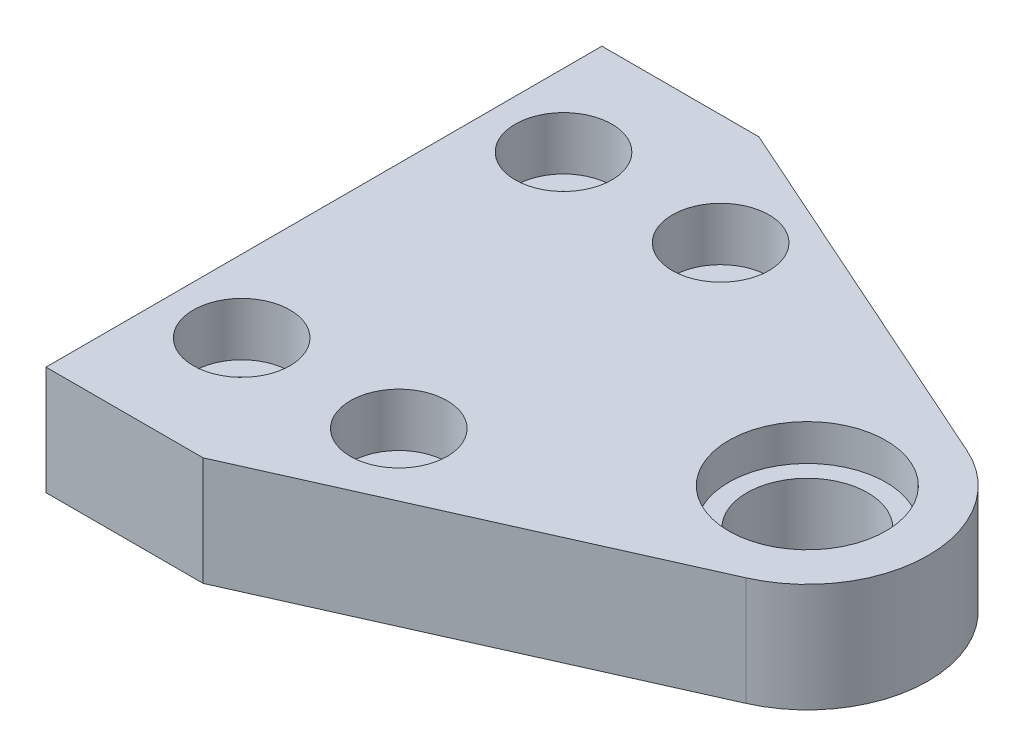
SolidWorks part; units mm, degrees
ref_plane "정면" through (0, 0, 0) normal (0, 0, 1) x (1, 0, 0)
ref_plane "윗면" through (0, 0, 0) normal (0, 1, 0) x (1, 0, 0)
ref_plane "우측면" through (0, 0, 0) normal (1, 0, 0) x (0, 0, -1)
sketch "스케치1" plane through (0, 0, 0) normal (0, 1, 0) x (1, 0, 0)
  line L0 (0, 0) -> (0, 23)
  line L1 (0, 23) -> (13, 23)
  line L2 (13, 23) -> (44.0753, 9.1319)
  line L4 (44.0753, -9.1319) -> (13, -23)
  line L5 (13, -23) -> (0, -23)
  line L6 (0, -23) -> (0, 0)
  arc A0 (44.0753, -9.1319) -> (44.0753, 9.1319) centre (40, 0) ccw
  point P10 (0, 0)
  point P11 (0, 0)
  point P12 (0, 0)
  point P13 (0, 0)
  point P14 (0, 0)
  point P15 (0, 0)
  point P16 (0, 0)
  point P17 (0, 0)
  point P18 (42.51, 0)
  point P19 (0, 0)
  point P20 (0, 0)
  point P21 (0, 0)
  dimension "D3" = 20
  dimension "D1" = 13
  dimension "D2" = 13
  dimension "D4" = 23
  dimension "D5" = 40
extrude "보스-돌출1" add sketch "스케치1" along normal blind 9
sketch "스케치2" plane through (0, 0, 0) normal (0, -1, 0) x (1, 0, 0)
  line L0 (0, -23) -> (0, 23) construction
  line L1 (0, -5) -> (24, -5)
  line L2 (0, -5) -> (0, 5)
  line L3 (0, 5) -> (24, 5)
  line L4 (24, -5) -> (24, 5)
  dimension "D1" = 5
  dimension "D2" = 10
  dimension "D3" = 24
extrude "보스-돌출2" add sketch "스케치2" along normal blind 3
hole_wizard "M4 소켓 머리 캡 나사용 카운터보어1" positions "스케치3" profile "스케치4" counterbore size "M4" standard "KS"
sketch "스케치3" plane through (0, 9, 0) normal (0, 1, 0) x (1, 0, 0)
  line L0 (0, 23) -> (0, -23) construction
  point P0 (6, 13.8271)
  point P2 (19, 13.8271)
  point P4 (6, -12.8071)
  point P6 (19, -12.8071)
  point P9 (6.0727, 13.8271)
  point P10 (0, 0)
  point P17 (14.573, 13.2604)
  point P18 (0, 0)
  point P19 (0, 0)
  point P20 (0, 0)
  point P25 (9.9262, -15.1872)
  dimension "D1" = 6
  dimension "D2" = 13
  dimension "D3" = 6
  dimension "D4" = 13
sketch "스케치4" plane through (6, 9, -13.8271) normal (1, 0, 0) x (0, 0, 1)
  line L0 (0, 0) -> (0, 10.3519)
  line L1 (0, 10.3519) -> (2.25, 9)
  line L2 (2.25, 9) -> (2.25, 4.4)
  line L3 (2.25, 4.4) -> (4, 4.4)
  line L4 (4, 4.4) -> (4, 0)
  line L5 (4, 0) -> (0, 0)
  line L10 (0, 10.3519) -> (-2.25, 9) construction
  line L11 (0, -6.35) -> (0, 107.95) construction
  dimension "구멍 지름" = 4.5
  dimension "구멍 깊이" = 9
  dimension "카운터보어 지름" = 8
  dimension "카운터보어 깊이" = 4.4
  dimension "드릴 각도" = 118
hole_wizard "M4 소켓 머리 캡 나사용 카운터보어2" positions "스케치5" profile "스케치6" counterbore size "M4" standard "KS" end condition through all
sketch "스케치5" plane through (0, 9, 0) normal (0, 1, 0) x (1, 0, 0)
  arc A0 (44.0753, -9.1319) -> (44.0753, 9.1319) centre (40, 0) ccw construction
  point P0 (40, 0)
  point P3 (0, 0)
sketch "스케치6" plane through (40, 9, 0) normal (1, 0, 0) x (0, 0, 1)
  line L0 (0, 0) -> (0, 12)
  line L1 (0, 12) -> (5, 12)
  line L3 (5, 12) -> (5, 3)
  line L4 (5, 3) -> (6.5, 3)
  line L5 (6.5, 3) -> (6.5, 0)
  line L7 (6.5, 0) -> (0, 0)
  line L11 (0, -6.35) -> (0, 107.95) construction
  dimension "관통 구멍 지름" = 10
  dimension "관통 구멍 깊이" = 12
  dimension "카운터보어 지름" = 13
  dimension "카운터보어 깊이" = 3
